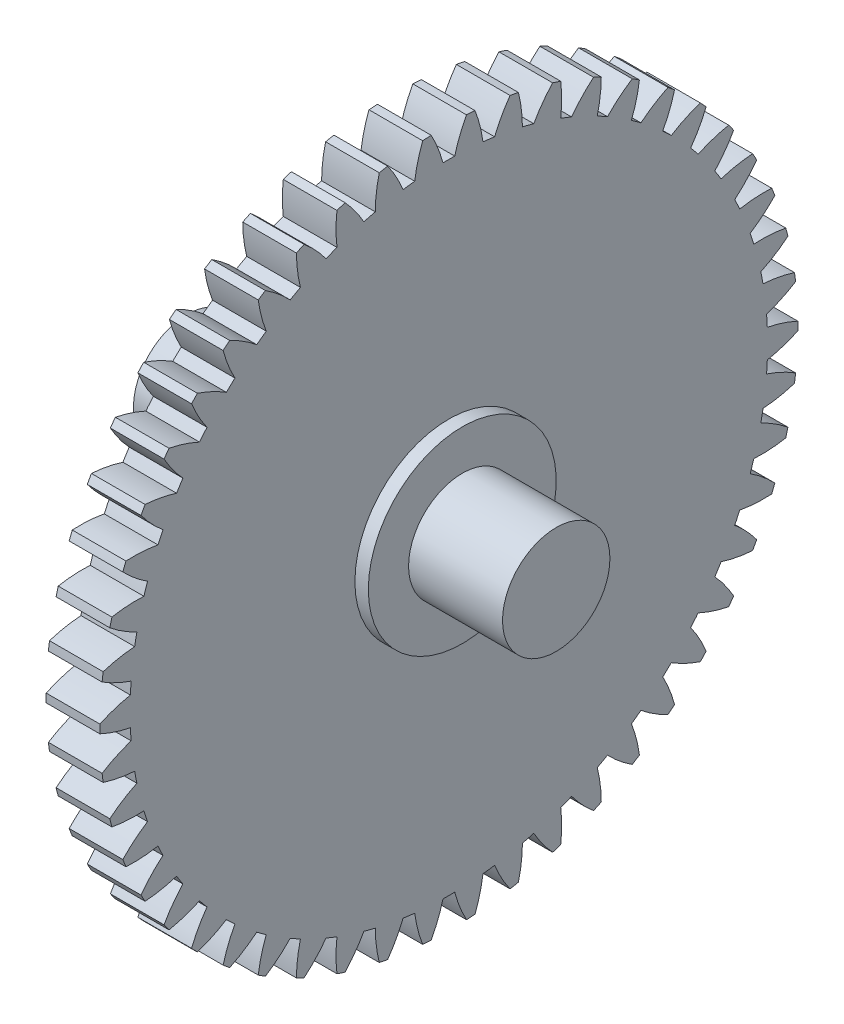
SolidWorks part; units mm, degrees
ref_plane "Plane1" through (0, 0, 0) normal (0, 0, 1) x (1, 0, 0)
ref_plane "Plane2" through (0, 0, 0) normal (0, 1, 0) x (1, 0, 0)
ref_plane "Plane3" through (0, 0, 0) normal (1, 0, 0) x (0, 0, -1)
sketch "HoldingSke" plane through (0, 0, 0) normal (0, 1, 0) x (1, 0, 0)
  line L0 (0, 0) -> (0.6428, -0.766)
  line L1 (-15, 0) -> (100, 0) construction
  line L2 (0, 0) -> (-2.1039, 2.3779)
  line L3 (0, 0) -> (-11.863, 4.5341)
  line L4 (0, 0) -> (5.5511, 6.6156)
  line L5 (0, 0) -> (-46.8476, -17.4728)
  line L6 (0, 0) -> (-3.3159, -2.2372)
  line L7 (-2.1039, 2.3779) -> (8.6586, 51.2061)
  line L8 (-76.2, 54.61) -> (-75.3, 54.61)
  line L9 (-71.009, 38.7566) -> (-53.1078, 45.2721)
  line L10 (-76.2, 71.12) -> (104.1128, 71.12)
  line L11 (0, 0) -> (-4, 0)
  line L12 (-76.2, 101.6) -> (-76.162, 101.6)
  line L13 (24.9733, 27.94) -> (52.9518, 28.4284)
  line L14 (24.9733, 27.94) -> (24.9743, 27.94)
  line L15 (24.9733, 27.94) -> (100.4006, 29.5858)
  line L16 (-63.627, -1) -> (-12.827, -1)
  circle A0 centre (0, 0) radius 2.5
  circle A1 centre (0, 0) radius 23.749
  circle A2 centre (0, 0) radius 37.5
  circle A3 centre (0, 0) radius 2.5
  dimension "MHD" = 47.498
  dimension "Hub_dia" = 75
  dimension "Bore" = 5
  dimension "MBD" = 5
  dimension "Num_teeth" = 50
  dimension "Pitch" = 1
  dimension "Overall_len" = 50
  dimension "Show_teeth" = 50
  dimension "Thickness" = 4
  dimension "OAL" = 50.0003
  dimension "T_dim" = 0.9
  dimension "Ap" = 20
  dimension "H" = 19.05
  dimension "Pitch_radius" = 180.3128
  dimension "Width" = 4
  dimension "Backlash" = 0.038
  dimension "Addendum_fac" = 1
  dimension "Dedendum_fac" = 1.25
  dimension "Clearance_fac" = 0.25
  dimension "Dedendum_add" = 0.001
  dimension "Module" = 1
sketch "BasProSke" plane through (0, 0, 0) normal (0, 1, 0) x (1, 0, 0)
  line L0 (-10, 0) -> (60, 0) construction
  line L1 (0, 0) -> (0, 26)
  line L2 (0, 0) -> (4, 0)
  line L3 (4, 0) -> (4, 26)
  line L4 (4, 26) -> (0, 26)
  dimension "Thickness" = 4
  dimension "Diameter" = 52
revolve "Base-Revolve" add sketch "BasProSke" angle 360 about L0
sketch "TooCutSke" plane through (0, 0, 0) normal (1, 0, 0) x (0, 0, -1)
  line L1 (0, 0) -> (0, 107) construction
  line L2 (0, 0) -> (-0.8518, 24.9855) construction
  line L3 (0, 0) -> (-3.1382, 49.8807) construction
  line L4 (-0.8518, 24.9855) -> (-1.5691, 24.9404) construction
  arc A0 (0.4377, 23.745) -> (-0.4377, 23.745) centre (0, 0) ccw
  arc A1 (1.3294, 25.9914) -> (-1.3294, 25.9914) centre (0, 0) ccw
  circle A2 centre (0, 0) radius 25 construction
  circle A3 centre (0, 0) radius 23.4923 construction
  arc A4 (-0.4377, 23.745) -> (-1.3294, 25.9914) centre (-10.1099, 21.2056) ccw
  arc A5 (1.3294, 25.9914) -> (0.4377, 23.745) centre (10.1099, 21.2056) ccw
  dimension "Root_dia" = 47.498
  dimension "Overcut_dia" = 52.0508
  dimension "Pitch_dia" = 50
  dimension "Base_dia" = 46.9846
  dimension "Flank_rad" = 10
  dimension "Half_ang" = 3.6
  dimension "Half_CT" = 0.7188
extrude "ToothCut" cut sketch "TooCutSke" along normal through all
fillet "Breaks" [suppressed] radius 0.02
fillet "RootFillets" [suppressed] radius 0.251
pattern_circular "TeethCuts" count 50 every 7.2 about axis through (-10, 0, 0) along (1, 0, 0) of "ToothCut", "RootFillets", "Breaks"
sketch "HubNeaOneSke" plane through (0, 0, 0) normal (-1, 0, 0) x (0, 0, 1)
  circle A0 centre (0, 0) radius 23.749
  dimension "Diameter" = 47.498
extrude "HubNearOne" [suppressed] add sketch "HubNeaOneSke" along normal blind 46.0003
sketch "HubNeaBotSke" plane through (0, 0, 0) normal (-1, 0, 0) x (0, 0, 1)
  circle A0 centre (0, 0) radius 23.749
  dimension "Diameter" = 47.498
extrude "HubNearBoth" [suppressed] add sketch "HubNeaBotSke" along normal blind 23.0001
ref_plane "FarPln" through (4, 0, 0) normal (1, 0, 0) x (0, 0, -1)
sketch "HubFarSke" plane through (4, 0, 0) normal (1, 0, 0) x (0, 0, -1)
  circle A0 centre (0, 0) radius 23.749
  dimension "Diameter" = 47.498
extrude "HubFar" [suppressed] add sketch "HubFarSke" along normal blind 23.0001
sketch "BorSke" plane through (0, 0, 0) normal (1, 0, 0) x (0, 0, -1)
  circle A0 centre (0, 0) radius 7
  dimension "Diameter" = 14
extrude "Boss-Extrude1" add sketch "BorSke" along normal up to surface (5 mm away) and the other way up to surface (8.5 mm away)
sketch "Sketch1" plane through (5, 0, 0) normal (1, 0, 0) x (0, 0, -1)
  circle A0 centre (0, 0) radius 4
  dimension "D1" = 8
extrude "Boss-Extrude2" add sketch "Sketch1" along normal up to surface (7 mm away) and the other way up to surface (20.5 mm away)
equation "' \"Module@HoldingSke\" = 6.35"
equation "' \"Num_teeth@HoldingSke\" = 12"
equation "' \"Ap@HoldingSke\" =  20"
equation "' \"Ap@HoldingSke\" = 20"
equation "' \"Width@HoldingSke\" = 0.5 * 25.4"
equation "' \"Hub_dia@HoldingSke\"= 1 * 25.4"
equation "' \"Hub_dia@HoldingSke\" = 1 * 25.4"
equation "' \"Overall_len@HoldingSke\" = 1.0 * 25.4"
equation "' \"Bore@HoldingSke\" = 0.75 * 25.4"
equation "' \"T_dim@HoldingSke\" = 0.1 * 25.4"
equation "' \"Width@KeySke\" = 0.25 * 25.4"
equation "' \"Show_teeth@HoldingSke\" = 13"
equation "' \"Backlash@HoldingSke\" = 0.009 * 25.4"
equation "' \"Addendum_fac@HoldingSke\" = 1.0"
equation "' \"Dedendum_fac@HoldingSke\" = 1.25"
equation "' \"Dedendum_add@HoldingSke\" = 0.00005 * 25.4"
equation "' \"Clearance_fac@HoldingSke\" = 0.25"
equation "\"Pitch@HoldingSke\" = 1 / \"Module@HoldingSke\""
equation "\"Overcut_dia@TooCutSke\" = (\"Num_teeth@HoldingSke\" + 2 * \"Addendum_fac@HoldingSke\") / \"Pitch@HoldingSke\" + 0.002 * 25.4"
equation "\"Pitch_dia@TooCutSke\" = \"Num_teeth@HoldingSke\" / \"Pitch@HoldingSke\""
equation "\"Base_dia@TooCutSke\" = \"Num_teeth@HoldingSke\" / \"Pitch@HoldingSke\" * cos((\"Ap@HoldingSke\"  * 3.14159265 / 180))"
equation "\"Root_dia@TooCutSke\" = (\"Num_teeth@HoldingSke\" + 2) / \"Pitch@HoldingSke\" - 2 * (\"Addendum_fac@HoldingSke\" + \"Dedendum_fac@HoldingSke\") / \"Pitch@HoldingSke\" - \"Dedendum_add@HoldingSke\" * 2"
equation "\"Half_ang@TooCutSke\" = 180 / \"Num_teeth@HoldingSke\""
equation "\"Half_CT@TooCutSke\" = \"Num_teeth@HoldingSke\" / \"Pitch@HoldingSke\" * sin((3.14159265 / 2 / \"Num_teeth@HoldingSke\")) / 2 - 7 * \"Backlash@HoldingSke\" / 4"
equation "\"Flank_rad@TooCutSke\" = \"Num_teeth@HoldingSke\" / \"Pitch@HoldingSke\" / 5"
equation "\"Radius@RootFillets\" = \"Clearance_fac@HoldingSke\" / \"Pitch@HoldingSke\" + \"Dedendum_add@HoldingSke\""
equation "\"Break_rad@Breaks\" = 0.02 / \"Pitch@HoldingSke\""
equation "\"Thickness@HoldingSke\" = \"Width@HoldingSke\""
equation "\"OAL@HoldingSke\" = \"Thickness@HoldingSke\""
equation "\"MHD@HoldingSke\" = (\"Num_teeth@HoldingSke\" + 2) / \"Pitch@HoldingSke\" - 2 * (\"Addendum_fac@HoldingSke\" + \"Dedendum_fac@HoldingSke\")  / \"Pitch@HoldingSke\" - \"Dedendum_add@HoldingSke\" * 2"
equation "\"MBD@HoldingSke\" = (\"Num_teeth@HoldingSke\" + 2) / \"Pitch@HoldingSke\" - 2 * (\"Addendum_fac@HoldingSke\" + \"Dedendum_fac@HoldingSke\")  / \"Pitch@HoldingSke\" - \"Dedendum_add@HoldingSke\" * 2 - 0.002 * 25.4"
equation "\"MHD@HoldingSke\" = ((sgn( \"MHD@HoldingSke\" - \"Hub_dia@HoldingSke\" )-1)*( \"MHD@HoldingSke\" - \"Hub_dia@HoldingSke\" ))/-2+ \"Hub_dia@HoldingSke\""
equation "\"MBD@HoldingSke\" = ((sgn( \"MBD@HoldingSke\" - \"Bore@HoldingSke\" )-1)*( \"MBD@HoldingSke\" - \"Bore@HoldingSke\" ))/-2+ \"Bore@HoldingSke\""
equation "\"OAL@HoldingSke\" = ((sgn( \"OAL@HoldingSke\" - \"Overall_len@HoldingSke\" )+1)*( \"OAL@HoldingSke\" - \"Overall_len@HoldingSke\" ))/2 + \"Overall_len@HoldingSke\" + 0.000002 * 25.4"
equation "\"Num_teeth@TeethCuts\" = int( \"Show_teeth@HoldingSke\" ) + 1"
equation "\"Num_teeth@TeethCuts\" = ((sgn( \"Num_teeth@TeethCuts\" - \"Num_teeth@HoldingSke\" )-1)*( \"Num_teeth@TeethCuts\" - \"Num_teeth@HoldingSke\" ))/-2+ \"Num_teeth@HoldingSke\""
equation "\"Num_teeth@TeethCuts\" = ((sgn( \"Num_teeth@TeethCuts\" - 2.0)+1)*( \"Num_teeth@TeethCuts\" - 2.0))/2 +2.0"
equation "\"Angle@TeethCuts\" = 360.0 / \"Num_teeth@HoldingSke\""
equation "\"Diameter@BasProSke\" = (\"Num_teeth@HoldingSke\" + 2 * \"Addendum_fac@HoldingSke\") / \"Pitch@HoldingSke\""
equation "\"Thickness@BasProSke\"  = \"Thickness@HoldingSke\""
equation "' \"Fillet_rad@BasProSke\" =  \"Thickness@HoldingSke\" * 0.05"
equation "' \"Fillet_rad@BasProSke\" = \"Thickness@HoldingSke\" * 0.05"
equation "\"MHD@HoldingSke\" = ((sgn( \"MHD@HoldingSke\" - \"Root_dia@TooCutSke\" )-1)*( \"MHD@HoldingSke\" - \"Root_dia@TooCutSke\" ))/-2+ \"Root_dia@TooCutSke\""
equation "\"Diameter@HubNeaOneSke\" = \"MHD@HoldingSke\""
equation "\"Length@HubNearOne\" = \"OAL@HoldingSke\" - \"Thickness@BasProSke\""
equation "\"Diameter@HubNeaBotSke\" = \"MHD@HoldingSke\""
equation "\"Length@HubNearBoth\" = ( \"OAL@HoldingSke\" - \"Thickness@BasProSke\" ) / 2.0"
equation "\"Thickness@FarPln\" = \"Thickness@BasProSke\""
equation "\"Diameter@HubFarSke\" = \"MHD@HoldingSke\""
equation "\"Length@HubFar\" = ( \"OAL@HoldingSke\" - \"Thickness@BasProSke\" ) / 2.0"
